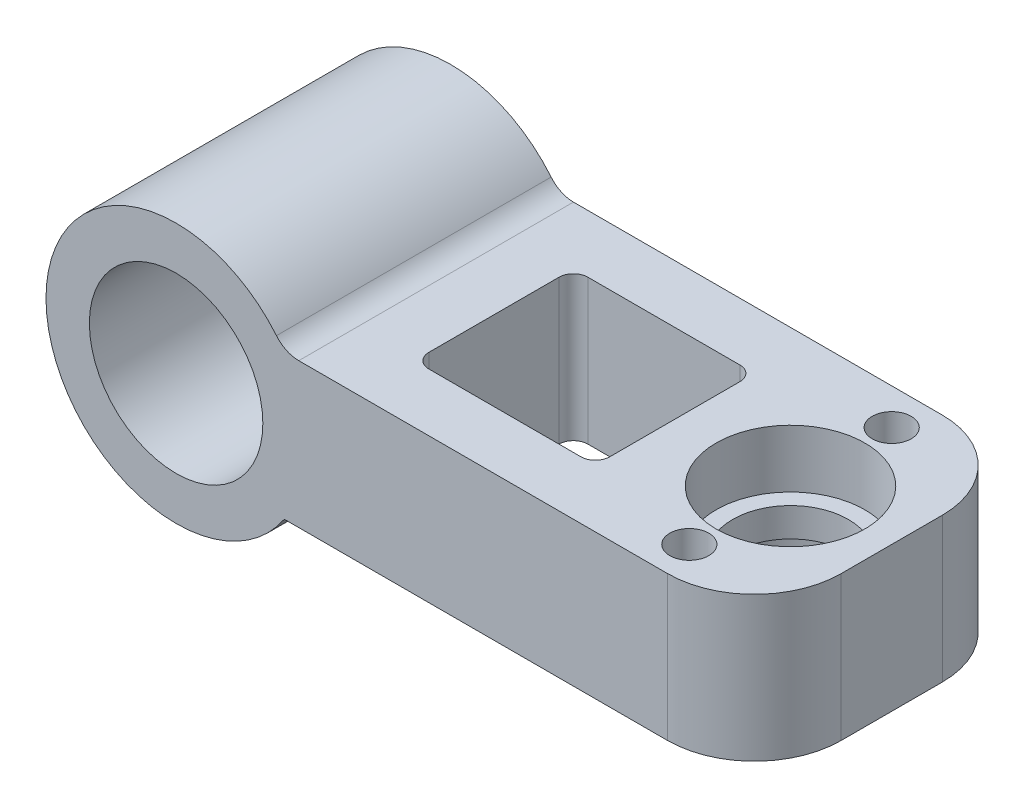
SolidWorks part; units mm, degrees
ref_plane "Front Plane" through (0, 0, 0) normal (0, 0, 1) x (1, 0, 0)
ref_plane "Top Plane" through (0, 0, 0) normal (0, 1, 0) x (1, 0, 0)
ref_plane "Right Plane" through (0, 0, 0) normal (1, 0, 0) x (0, 0, -1)
sketch "Sketch1" plane through (0, 0, 0) normal (0, 0, 1) x (1, 0, 0)
  circle A0 centre (0, 0) radius 6
  circle A1 centre (0, 0) radius 9
  dimension "D1" = 18
  dimension "D2" = 12
extrude "Main" add sketch "Sketch1" along normal mid plane 19
sketch "Sketch2" plane through (0, 0, 0) normal (0, 1, 0) x (1, 0, 0)
  line L0 (9, 9.5) -> (-9, 9.5) construction
  line L1 (0, 9.5) -> (40, 9.5)
  line L2 (0, 9.5) -> (0, -9.5)
  line L3 (0, -9.5) -> (40, -9.5)
  line L4 (40, 9.5) -> (40, -9.5)
  line L5 (-9, -9.5) -> (9, -9.5) construction
  line L7 (33, 7) -> (33, -7) construction
  circle A0 centre (33, 0) radius 4
  circle A1 centre (33, 7) radius 1.35
  circle A2 centre (33, -7) radius 1.35
  dimension "D4" = 8
  dimension "D5" = 2.7
  dimension "D2" = 40
  dimension "D3" = 7
  dimension "D6" = 14
extrude "BallSupportExtrusion" add sketch "Sketch2" along normal mid plane 10
sketch "Sketch3" plane through (0, 5, 0) normal (0, 1, 0) x (1, 0, 0)
  circle A0 centre (33, 0) radius 5.15
  dimension "D1" = 10.3
extrude "BallSupportHole" cut sketch "Sketch3" against normal blind 4
fillet "Fillet2" radius 2 1 edges at (7.4833, 5, 0)
sketch "Sketch5" plane through (0, 0, 9.5) normal (0, 0, 1) x (1, 0, 0)
  circle A0 centre (0, 0) radius 6
  dimension "D1" = 12
extrude "Cut-Extrude2" cut sketch "Sketch5" against normal through all
mirror "Mirror1" about plane through (0, 0, 0) normal (0, 1, 0) of "BallSupportHole"
sketch "Sketch6" plane through (0, 5, 0) normal (0, 1, 0) x (1, 0, 0)
  line L0 (40, 9.5) -> (8.4853, 9.5) construction
  line L1 (12.4853, 5.5) -> (25, 5.5)
  line L2 (12.4853, 5.5) -> (12.4853, -5.5)
  line L3 (12.4853, -5.5) -> (25, -5.5)
  line L4 (25, 5.5) -> (25, -5.5)
  line L5 (8.4853, -9.5) -> (40, -9.5) construction
  line L6 (8.4853, 9.5) -> (8.4853, -9.5) construction
  line L7 (40, -9.5) -> (40, 9.5) construction
  dimension "D1" = 4
  dimension "D2" = 4
  dimension "D3" = 4
  dimension "D4" = 15
extrude "Cut-Extrude3" cut sketch "Sketch6" against normal through all
fillet "Fillet3" radius 1 4 edges at (25, 0, -5.5) (12.4853, 0, -5.5) (25, 0, 5.5) (12.4853, 0, 5.5)
fillet "Fillet4" radius 6 2 edges at (40, 0, -9.5) (40, 0, 9.5)
